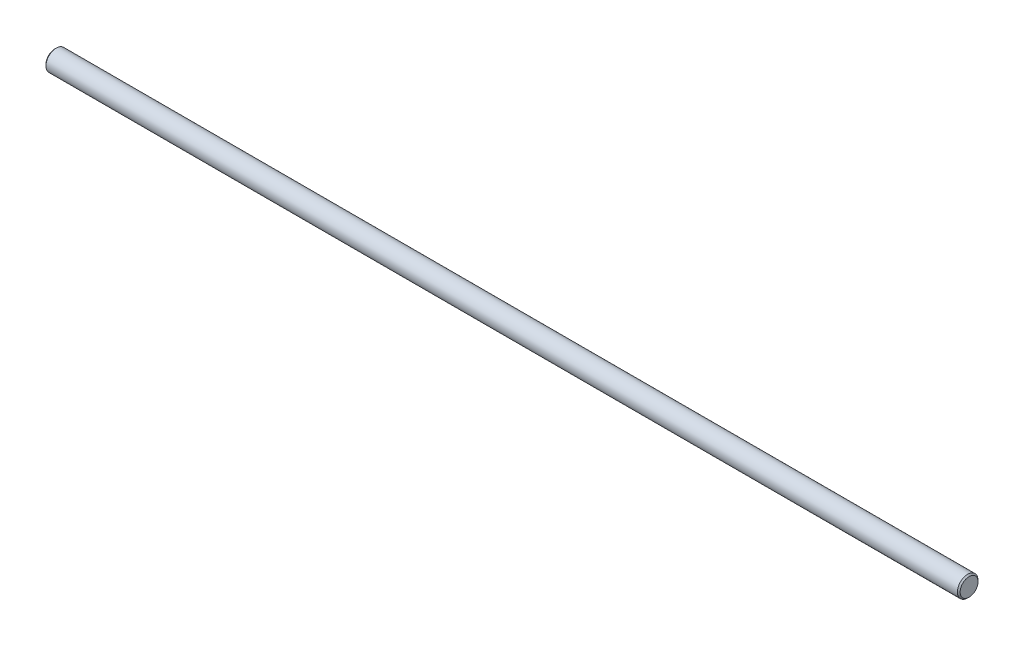
SolidWorks part; units mm, degrees
ref_plane "Plan de face" through (0, 0, 0) normal (0, 0, 1) x (1, 0, 0)
ref_plane "Plan de dessus" through (0, 0, 0) normal (0, 1, 0) x (1, 0, 0)
ref_plane "Plan de droite" through (0, 0, 0) normal (1, 0, 0) x (0, 0, -1)
sketch "Esquisse1" plane through (0, 0, 0) normal (1, 0, 0) x (0, 0, -1)
  circle A0 centre (0, 0) radius 1.5
extrude "Boss.-Extru.1" add sketch "Esquisse1" along normal blind 133
chamfer "Chanfrein1" distance 0.2 angle 45 2 edges at (0, 0, -1.5) (133, 0, -1.5)
